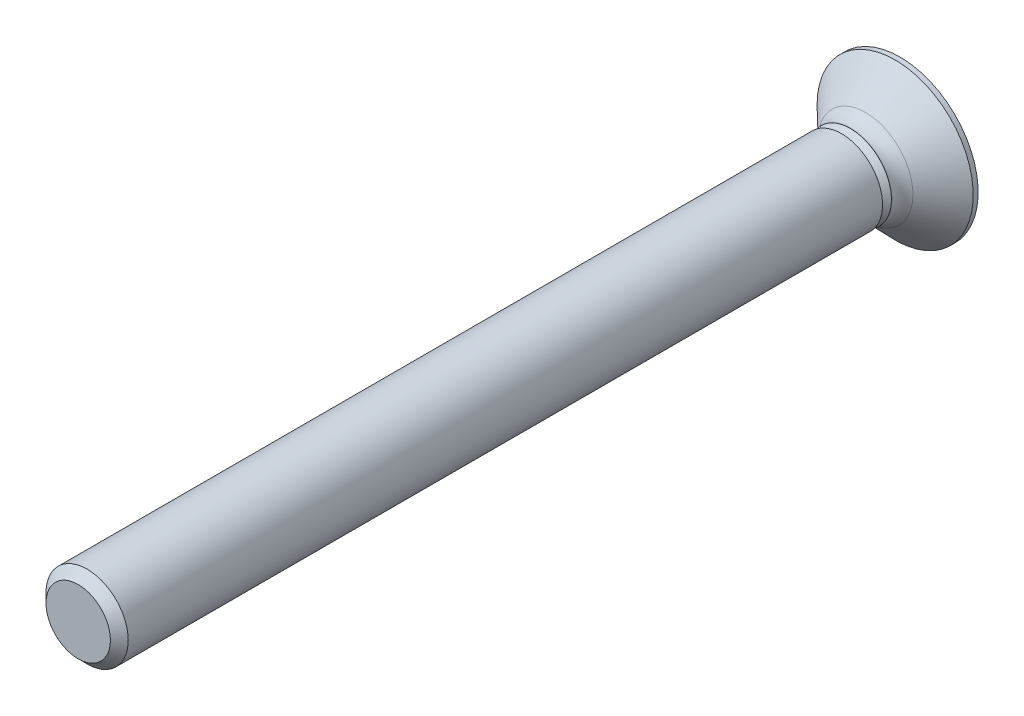
SolidWorks part; units mm, degrees
ref_plane "Front Plane" through (0, 0, 0) normal (0, 0, 1) x (1, 0, 0)
ref_plane "Top Plane" through (0, 0, 0) normal (0, 1, 0) x (1, 0, 0)
ref_plane "Right Plane" through (0, 0, 0) normal (1, 0, 0) x (0, 0, -1)
ref_plane "Plane1" through (0, 0, 0) normal (0, -1, 0) x (1, 0, 0)
sketch "Sketch1" plane through (0, 0, 0) normal (0, -1, 0) x (1, 0, 0)
  line L0 (1, 20) -> (0, 20)
  line L1 (0, 20) -> (0, 1.4265)
  line L2 (0, 1.4265) -> (1, 1.4265)
  line L3 (1, 1.4265) -> (1, 20)
  line L4 (0, 20) -> (0, 1.4265) construction
revolve "Revolve1" add sketch "Sketch1" angle 360 about L4
sketch "Sketch2" plane through (0, 0, 1.4265) normal (0, 0, -1) x (-1, 0, 0)
  circle A0 centre (0, 0) radius 0.7835
extrude "Boss-Extrude1" add sketch "Sketch2" along normal blind 0.2165 draft 45 draft outward yes
sketch "Sketch3" plane through (0, 0, 1.21) normal (0, 0, -1) x (-1, 0, 0)
  circle A0 centre (0, 0) radius 1
extrude "Boss-Extrude2" add sketch "Sketch3" along normal blind 0.2224
sketch "Sketch4" plane through (0, 0, 0.9876) normal (0, 0, -1) x (-1, 0, 0)
  circle A0 centre (0, 0) radius 1
extrude "Boss-Extrude3" add sketch "Sketch4" along normal blind 0.8676 draft 46.049 draft outward yes
sketch "Sketch5" plane through (0, 0, 0.12) normal (0, 0, -1) x (-1, 0, 0)
  circle A0 centre (0, 0) radius 1.9
extrude "Boss-Extrude4" add sketch "Sketch5" along normal blind 0.12
sketch "Sketch6" plane through (0, 0, 0) normal (0, 0, -1) x (-1, 0, 0)
  line L0 (-0.95, -0.1583) -> (-0.4101, -0.4101)
  line L1 (-0.4101, -0.4101) -> (-0.1583, -0.95)
  line L2 (-0.1583, -0.95) -> (0.1583, -0.95)
  line L3 (0.1583, -0.95) -> (0.4101, -0.4101)
  line L4 (0.4101, -0.4101) -> (0.95, -0.1583)
  line L5 (0.95, -0.1583) -> (0.95, 0.1583)
  line L6 (0.95, 0.1583) -> (0.4101, 0.4101)
  line L7 (0.4101, 0.4101) -> (0.1583, 0.95)
  line L8 (0.1583, 0.95) -> (-0.1583, 0.95)
  line L9 (-0.1583, 0.95) -> (-0.4101, 0.4101)
  line L10 (-0.4101, 0.4101) -> (-0.95, 0.1583)
  line L11 (-0.95, 0.1583) -> (-0.95, -0.1583)
extrude "Cut-Extrude1" cut sketch "Sketch6" against normal blind 0.9 draft 15
chamfer "Chamfer1" distance 0.2165 angle 45 1 edges at (-1, 0, 20)
fillet "Fillet1" radius 0.5 1 edges at (-1, 0, 0.9876)
ref_plane "Plane2" through (0.95, 0.1583, 0) normal (0, -1, 0) x (-1, 0, 0)
scale "Scale1" scale about centroid uniform scaling yes scale factor 3.125
